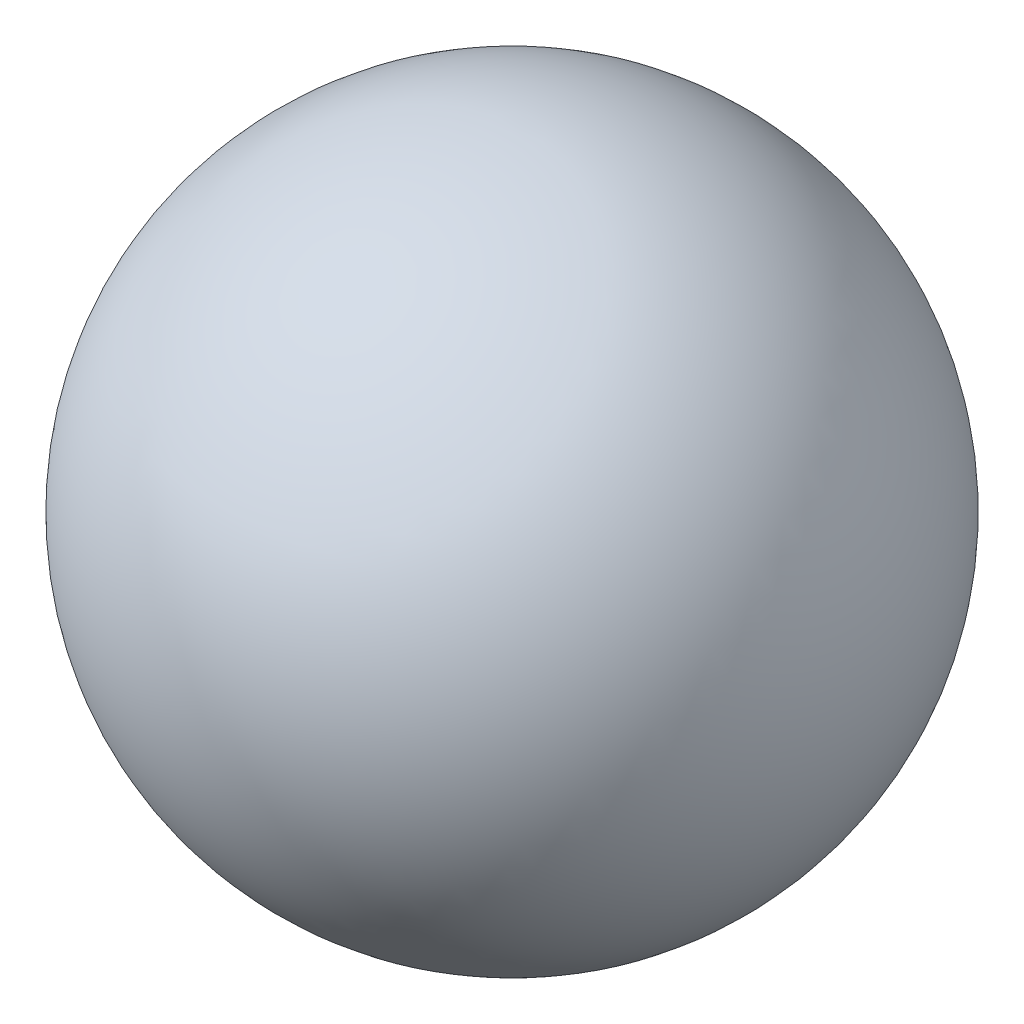
SolidWorks part; units mm, degrees
ref_plane "Plan de face" through (0, 0, 0) normal (0, 0, 1) x (1, 0, 0)
ref_plane "Plan de dessus" through (0, 0, 0) normal (0, 1, 0) x (1, 0, 0)
ref_plane "Plan de droite" through (0, 0, 0) normal (1, 0, 0) x (0, 0, -1)
sketch "Esquisse1" plane through (0, 0, 0) normal (0, 0, 1) x (1, 0, 0)
  line L0 (0, 40) -> (0, 0)
  line L1 (0, 51.2497) -> (0, -12.2711) construction
  arc A0 (0, 40) -> (0, 0) centre (0, 20) ccw
  dimension "D1" = 20
revolve "Révolution1" add sketch "Esquisse1" angle 360 about L1
